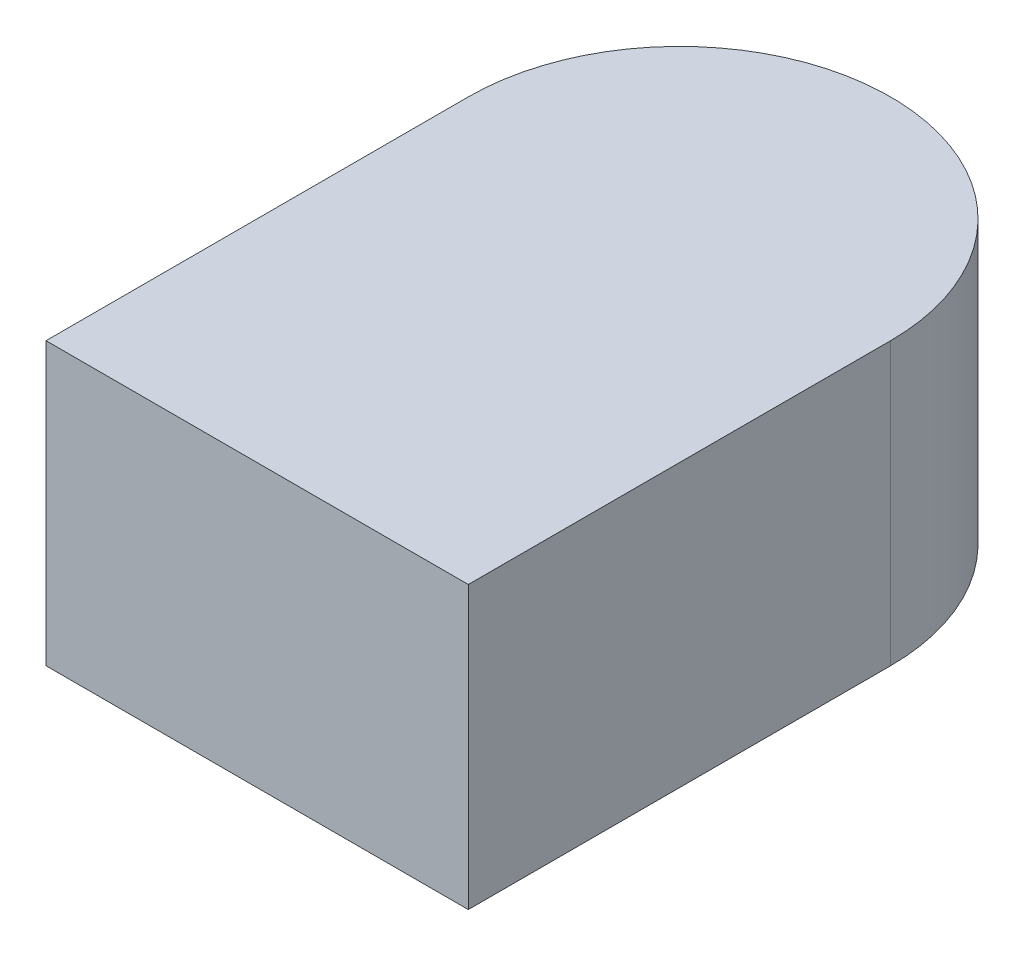
SolidWorks part; units mm, degrees
ref_plane "Front Plane" through (0, 0, 0) normal (0, 0, 1) x (1, 0, 0)
ref_plane "Top Plane" through (0, 0, 0) normal (0, 1, 0) x (1, 0, 0)
ref_plane "Right Plane" through (0, 0, 0) normal (1, 0, 0) x (0, 0, -1)
sketch "Sketch1" plane through (0, 0, 0) normal (0, 1, 0) x (1, 0, 0)
  line L1 (-0.15, -0.15) -> (0.15, -0.15)
  line L2 (-0.15, -0.15) -> (-0.15, 0.15)
  line L3 (-0.15, 0.15) -> (0.15, 0.15) construction
  line L4 (0.15, -0.15) -> (0.15, 0.15)
  line L5 (-0.15, -0.15) -> (0.15, 0.15) construction
  line L6 (-0.15, 0.15) -> (0.15, -0.15) construction
  arc A0 (0.15, 0.15) -> (-0.15, 0.15) centre (0, 0.15) ccw
  point P0 (0, 0)
  point P7 (0, 0.3)
  dimension "D1" = 0.3
  dimension "D2" = 0.45
extrude "Boss-Extrude1" add sketch "Sketch1" along normal blind 0.2
